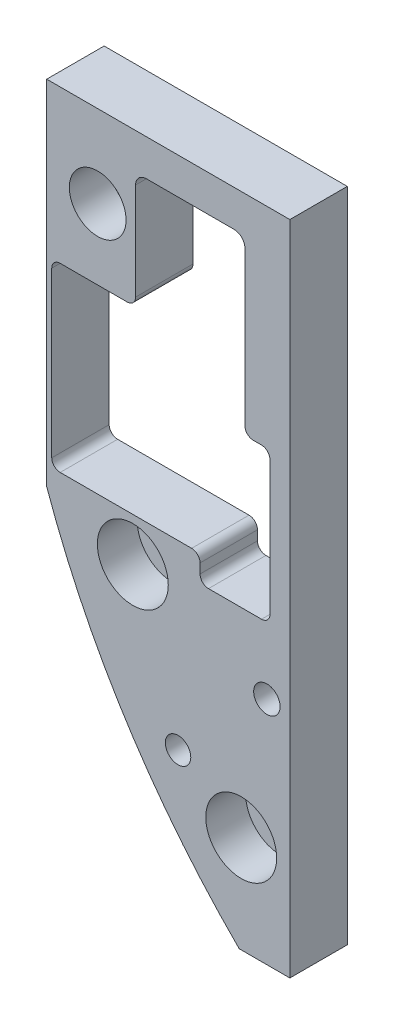
SolidWorks part; units mm, degrees
material "PET"
ref_plane "Front" through (0, 0, 0) normal (0, 0, 1) x (1, 0, 0)
ref_plane "Top" through (0, 0, 0) normal (0, 1, 0) x (1, 0, 0)
ref_plane "Right" through (0, 0, 0) normal (1, 0, 0) x (0, 0, -1)
sketch "Sketch1" plane through (0, 0, 0) normal (0, 0, 1) x (1, 0, 0)
  line L4 (0, -17.78) -> (-45.72, -17.78)
  line L5 (-45.72, -17.78) -> (-45.72, -84.1375)
  line L6 (-9.525, -141.2875) -> (0, -141.2875)
  line L7 (0, -141.2875) -> (0, -17.78)
  line L8 (0, -17.78) -> (-45.72, -17.78)
  line L9 (-45.72, -17.78) -> (-45.72, -84.1375)
  line L10 (-9.525, -141.2875) -> (0, -141.2875)
  line L11 (0, -141.2875) -> (0, -17.78)
  line L17 (-30.5943, -46.5015) -> (-43.1857, -46.5015)
  line L18 (-44.7732, -48.089) -> (-44.7732, -78.9652)
  line L19 (-43.1857, -80.5527) -> (-18.4742, -80.5527)
  line L20 (-16.8867, -82.1402) -> (-16.8867, -83.9371)
  line L21 (-15.2992, -85.5246) -> (-5.3275, -85.5246)
  line L22 (-3.74, -83.9371) -> (-3.74, -58.7502)
  line L23 (-6.8707, -57.1627) -> (-5.3275, -57.1627)
  line L80 (-8.4582, -55.1307) -> (-8.4582, -26.6573)
  line L81 (-26.9748, -57.1627) -> (-10.4902, -57.1627)
  line L82 (-29.0068, -26.6573) -> (-29.0068, -55.1307)
  line L83 (-10.4902, -24.6253) -> (-26.9748, -24.6253)
  line L84 (-8.4582, -55.5752) -> (-8.4582, -26.6573)
  line L86 (-29.0068, -26.6573) -> (-29.0068, -44.914)
  line L87 (-10.4902, -24.6253) -> (-26.9748, -24.6253)
  circle A1 centre (-36.1315, -33.274) radius 2.1526
  circle A2 centre (-36.1315, -33.274) radius 2.1527
  circle A3 centre (-29.5275, -88.7095) radius 2.1526
  circle A4 centre (-29.5275, -88.7095) radius 2.1527
  circle A5 centre (-9.144, -122.9995) radius 2.1526
  circle A6 centre (-9.144, -122.9995) radius 2.1527
  arc A7 (-45.72, -84.1375) -> (-9.525, -141.2875) centre (97.9169, -33.2042) ccw
  arc A8 (-45.72, -84.1375) -> (-9.525, -141.2875) centre (97.9169, -33.2042) ccw
  arc A9 (-3.74, -58.7502) -> (-5.3275, -57.1627) centre (-5.3275, -58.7502) ccw
  arc A10 (-8.4582, -55.5752) -> (-6.8707, -57.1627) centre (-6.8707, -55.5752) ccw
  arc A11 (-30.5943, -46.5015) -> (-29.0068, -44.914) centre (-30.5943, -44.914) ccw
  arc A12 (-43.1857, -46.5015) -> (-44.7732, -48.089) centre (-43.1857, -48.089) ccw
  arc A13 (-44.7732, -78.9652) -> (-43.1857, -80.5527) centre (-43.1857, -78.9652) ccw
  arc A14 (-18.4742, -80.5527) -> (-16.8867, -82.1402) centre (-18.4742, -82.1402) cw
  arc A15 (-16.8867, -83.9371) -> (-15.2992, -85.5246) centre (-15.2992, -83.9371) ccw
  arc A16 (-8.4582, -26.6573) -> (-10.4902, -24.6253) centre (-10.4902, -26.6573) ccw
  arc A17 (-10.4902, -57.1627) -> (-8.4582, -55.1307) centre (-10.4902, -55.1307) ccw
  arc A18 (-29.0068, -55.1307) -> (-26.9748, -57.1627) centre (-26.9748, -55.1307) ccw
  arc A19 (-26.9748, -24.6253) -> (-29.0068, -26.6573) centre (-26.9748, -26.6573) ccw
  arc A20 (-8.4582, -26.6573) -> (-10.4902, -24.6253) centre (-10.4902, -26.6573) ccw
  arc A23 (-26.9748, -24.6253) -> (-29.0068, -26.6573) centre (-26.9748, -26.6573) ccw
  arc A24 (-5.3275, -85.5246) -> (-3.74, -83.9371) centre (-5.3275, -83.9371) ccw
  circle A25 centre (-4.3174, -98.0359) radius 2.487
  circle A26 centre (-21.0247, -114.6804) radius 2.3945
  dimension "D5" = 1.5875
  dimension "D1" = 0
  dimension "D2" = 0
  dimension "D3" = 0
  dimension "D4" = 0
  dimension "D9" = 1.27
extrude "Boss-Extrude1" add sketch "Sketch1" along normal blind 10.8 contours L8 L9 A8 L10 L11
sketch "Sketch3" plane through (0, 0, 10.8) normal (0, 0, 1) x (1, 0, 0)
  circle A0 centre (-9.144, -122.9995) radius 6.6675
  circle A1 centre (-29.5275, -88.7095) radius 6.6675
  circle A3 centre (-36.1315, -33.274) radius 5.334
  dimension "D1" = 10.668
  dimension "D2" = 13.335
  dimension "D3" = 13.335
extrude "Cut-Extrude1" cut sketch "Sketch3" against normal blind 7.5
